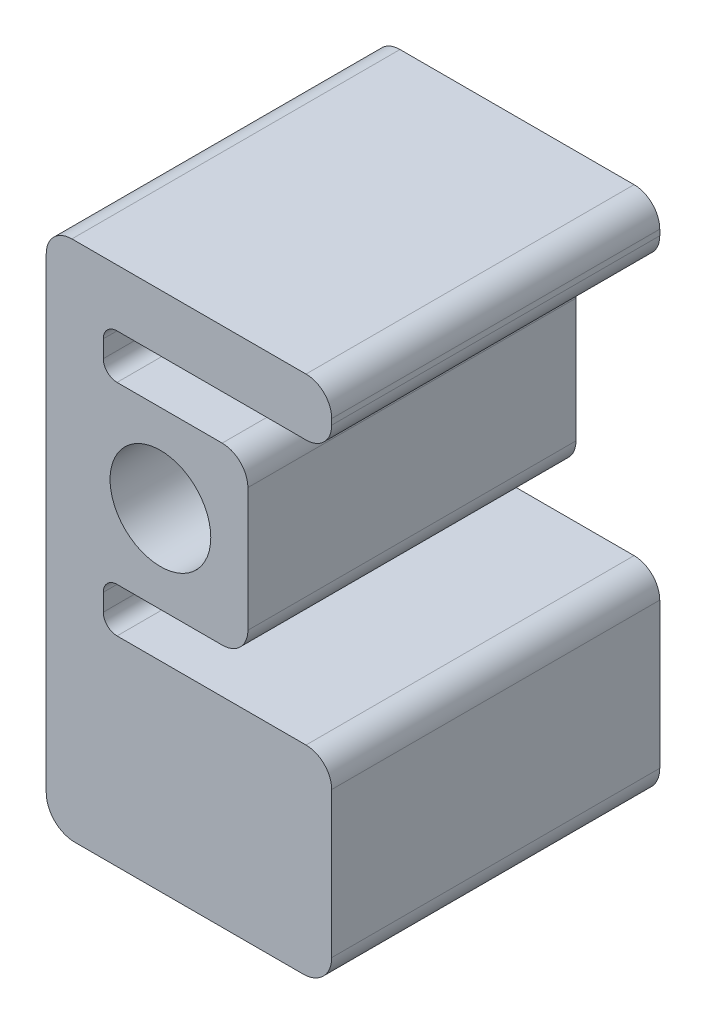
SolidWorks part; units mm, degrees
material "Pink Foam"
ref_plane "Front Plane" through (0, 0, 0) normal (0, 0, 1) x (1, 0, 0)
ref_plane "Top Plane" through (0, 0, 0) normal (0, 1, 0) x (1, 0, 0)
ref_plane "Right Plane" through (0, 0, 0) normal (1, 0, 0) x (0, 0, -1)
sketch "Sketch1" plane through (0, 0, 0) normal (0, 0, 1) x (1, 0, 0)
  line L0 (-25.4, -67.48) -> (-25.4, 36.365)
  line L2 (38.1, -67.48) -> (38.1, -35.095)
  line L3 (32.385, -29.38) -> (-9.652, -29.38)
  line L4 (-12.7, -26.332) -> (-12.7, -22.503)
  line L5 (-9.652, -19.455) -> (0, -19.455)
  line L6 (-9.652, 19.455) -> (0, 19.455)
  line L7 (-12.7, 22.503) -> (-12.7, 26.332)
  line L8 (-9.652, 29.38) -> (32.385, 29.38)
  line L9 (38.1, 35.095) -> (38.1, 36.365)
  line L10 (32.385, 42.08) -> (-19.685, 42.08)
  line L15 (0, -11.2) -> (0, -19.455) construction
  line L16 (0, 11.2) -> (0, 19.455) construction
  line L17 (11.2, 0) -> (19.455, 0) construction
  line L18 (0, 19.455) -> (13.74, 19.455)
  line L19 (19.455, 13.74) -> (19.455, 0)
  line L20 (19.455, 0) -> (19.455, -13.74)
  line L21 (13.74, -19.455) -> (0, -19.455)
  line L24 (31.75, -73.83) -> (-19.05, -73.83)
  circle A0 centre (0, 0) radius 11.2
  arc A3 (-19.685, 42.08) -> (-25.4, 36.365) centre (-19.685, 36.365) ccw
  arc A4 (38.1, 36.365) -> (32.385, 42.08) centre (32.385, 36.365) ccw
  arc A6 (32.385, 29.38) -> (38.1, 35.095) centre (32.385, 35.095) ccw
  arc A7 (38.1, -35.095) -> (32.385, -29.38) centre (32.385, -35.095) ccw
  arc A8 (19.455, -13.74) -> (13.74, -19.455) centre (13.74, -13.74) cw
  arc A9 (13.74, 19.455) -> (19.455, 13.74) centre (13.74, 13.74) cw
  arc A10 (-12.7, 26.332) -> (-9.652, 29.38) centre (-9.652, 26.332) cw
  arc A11 (-9.652, 19.455) -> (-12.7, 22.503) centre (-9.652, 22.503) cw
  arc A12 (-12.7, -22.503) -> (-9.652, -19.455) centre (-9.652, -22.503) cw
  arc A13 (-9.652, -29.38) -> (-12.7, -26.332) centre (-9.652, -26.332) cw
  arc A14 (31.75, -73.83) -> (38.1, -67.48) centre (31.75, -67.48) ccw
  arc A15 (-19.05, -73.83) -> (-25.4, -67.48) centre (-19.05, -67.48) cw
  point P12 (0, 11.2)
  point P20 (0, -11.2)
  point P22 (11.2, 0)
  point P45 (-12.7, 29.38)
  point P48 (-12.7, 19.455)
  point P53 (-12.7, -29.38)
  point P57 (38.1, -73.83)
  point P60 (38.1, -73.83)
  point P63 (-25.4, -73.83)
  dimension "D1" = 22.4
  dimension "D11" = 3.048
  dimension "D9" = 5.715
  dimension "D14" = 5.715
  dimension "D12" = 6.35
  dimension "D2" = 25.4
  dimension "D3" = 8.255
  dimension "D4" = 9.925
  dimension "D5" = 44.45
  dimension "D6" = 9.925
  dimension "D7" = 12.7
  dimension "D8" = 12.7
  dimension "D10" = 63.5
extrude "Boss-Extrude1" add sketch "Sketch1" along normal blind 72.9717
